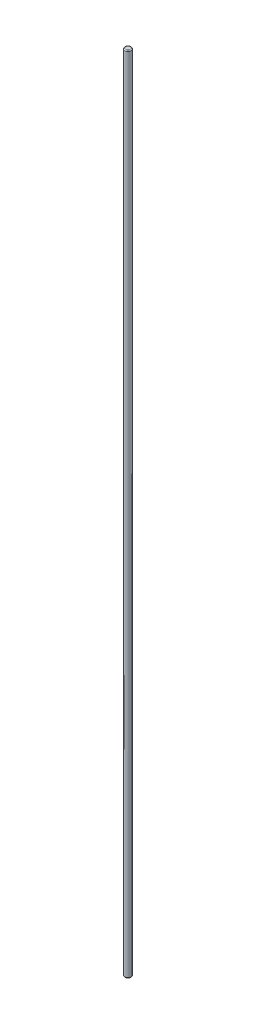
SolidWorks part; units mm, degrees
ref_plane "Front Plane" through (0, 0, 0) normal (0, 0, 1) x (1, 0, 0)
ref_plane "Top Plane" through (0, 0, 0) normal (0, 1, 0) x (1, 0, 0)
ref_plane "Right Plane" through (0, 0, 0) normal (1, 0, 0) x (0, 0, -1)
sketch "Sketch1" plane through (0, 0, 0) normal (0, 1, 0) x (1, 0, 0)
  circle A0 centre (0, 0) radius 11.25
  dimension "D1" = 22.5
extrude "Boss-Extrude1" add sketch "Sketch1" along normal blind 2850
fillet "Fillet1" radius 3 2 edges at (0, 0, 11.25) (0, 2850, 11.25)
